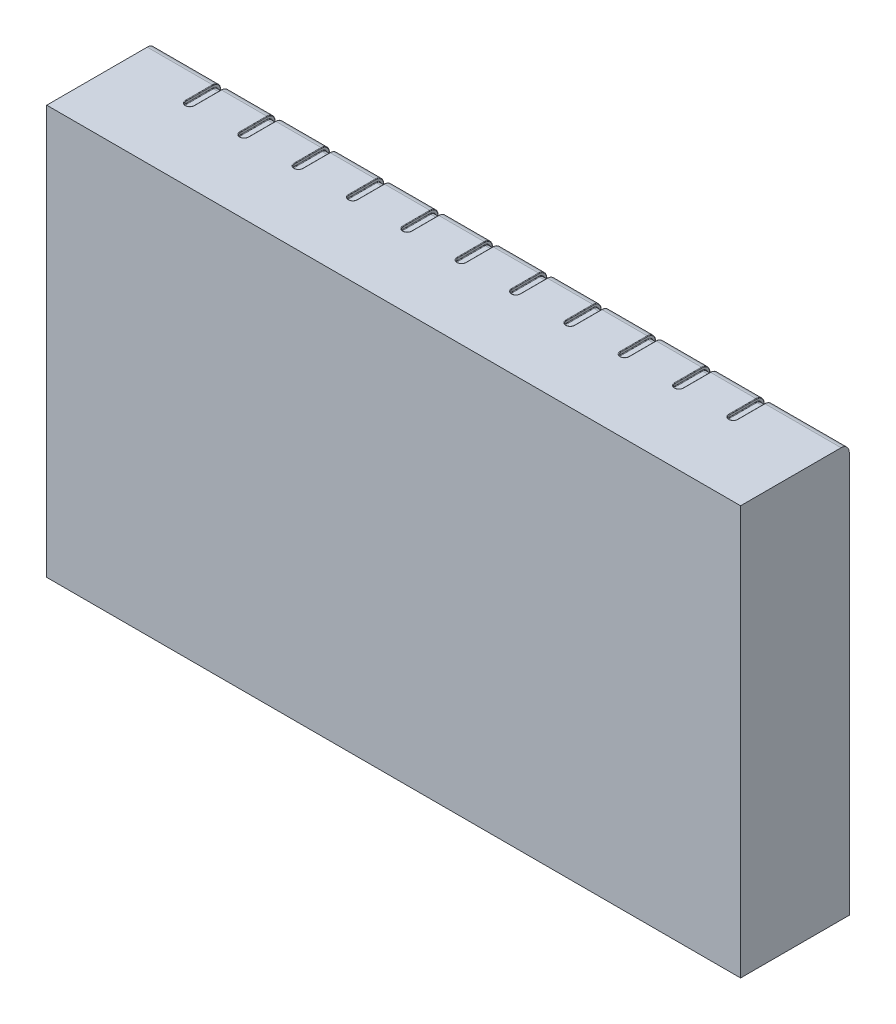
SolidWorks part; units mm, degrees
ref_plane "Plan de face" through (0, 0, 0) normal (0, 0, 1) x (1, 0, 0)
ref_plane "Plan de dessus" through (0, 0, 0) normal (0, 1, 0) x (1, 0, 0)
ref_plane "Plan de droite" through (0, 0, 0) normal (1, 0, 0) x (0, 0, -1)
sketch "Esquisse1" plane through (0, 0, 0) normal (0, 0, 1) x (1, 0, 0)
  line L1 (-127.6779, 75.255) -> (127.6779, 75.255)
  line L2 (-127.6779, 75.255) -> (-127.6779, -75.255)
  line L3 (-127.6779, -75.255) -> (127.6779, -75.255)
  line L4 (127.6779, 75.255) -> (127.6779, -75.255)
  line L5 (-127.6779, 75.255) -> (127.6779, -75.255) construction
  line L6 (-127.6779, -75.255) -> (127.6779, 75.255) construction
  point P0 (0, 0)
extrude "Boss.-Extru.1" add sketch "Esquisse1" along normal blind 40
fillet "Congé6" radius 3 1 edges at (0, 75.255, 0)
ref_plane "Plan1" through (97.6779, 0, 0) normal (1, 0, 0) x (0, 0, -1)
sketch "Esquisse2" plane through (97.6779, 0, 0) normal (1, 0, 0) x (0, 0, -1)
  line L6 (2, 72.255) -> (2, -75.255)
  line L7 (-40, 77.255) -> (-3, 77.255)
  line L8 (2, 72.255) -> (2, 62.255)
  line L9 (-13, 77.255) -> (-3, 77.255)
  line L13 (7, 82.255) -> (-13, 62.255) construction
  line L14 (7, 62.255) -> (-13, 82.255) construction
  arc A3 (2, 72.255) -> (-3, 77.255) centre (-3, 72.255) ccw
  arc A4 (2, 72.255) -> (-3, 77.255) centre (-3, 72.255) ccw
  dimension "D2" = 20
  dimension "D3" = 20
  dimension "D1" = 2
ref_plane "Plan2" through (97.6779, 77.255, 13) normal (0, 0, -1) x (-1, 0, 0)
sketch "Esquisse3" plane through (97.6779, 77.255, 13) normal (0, 0, -1) x (-1, 0, 0)
  line L1 (-1.8062, 2.8905) -> (1.1938, 2.8905)
  line L2 (-1.8062, 2.8905) -> (-1.8062, -3.1095)
  line L3 (-1.8062, -3.1095) -> (1.1938, -3.1095)
  line L4 (1.1938, 2.8905) -> (1.1938, -3.1095)
  line L5 (-1.8062, 2.8905) -> (1.1938, -3.1095) construction
  line L6 (-1.8062, -3.1095) -> (1.1938, 2.8905) construction
  point P0 (-0.3062, -0.1095)
  dimension "D1" = 3
  dimension "D2" = 6
sweep "Enlèvement de matière-Balayage1" cut profiles "Esquisse3" path "Esquisse2"
sketch "Esquisse4" plane through (0, 75.255, 0) normal (0, 1, 0) x (1, 0, 0)
  line L0 (96.4841, -13) -> (99.4841, -13) construction
  line L1 (99.4841, -13) -> (99.4841, -3) construction
  line L2 (96.4841, -3) -> (96.4841, -13) construction
  circle A0 centre (97.9841, -13) radius 1.5
extrude "Enlèv. mat.-Extru.1" cut sketch "Esquisse4" against normal up to surface (1.1095 mm away) up to face at (97.9841, 74.1454, 8)
sketch "Esquisse5" plane through (0, 0, 0) normal (0, 0, -1) x (-1, 0, 0)
  line L0 (-96.4841, 62.255) -> (-99.4841, 62.255) construction
  line L1 (-96.4841, 62.255) -> (-96.4841, 72.255) construction
  circle A0 centre (-97.9841, 62.255) radius 1.5
extrude "Enlèv. mat.-Extru.2" cut sketch "Esquisse5" against normal up to surface (1.1095 mm away) up to face at (97.9841, 67.255, 1.1095)
fillet "Congé7" radius 0.2 16 edges at (99.4841, 74.3763, 0.8787) (96.4841, 74.3763, 0.8787) (96.4841, 74.1454, 8) (99.4841, 73.5917, 1.6632) (99.4841, 67.255, 1.1095) (96.4841, 67.255, 1.1095) (96.4841, 73.5917, 1.6632) (96.4841, 75.255, 8) (96.4841, 67.255, 0) (99.4841, 75.255, 8) (99.4841, 67.255, 0) (99.4841, 74.1454, 8) (97.9841, 75.255, 14.5) (97.9841, 74.1454, 14.5) (97.9841, 60.755, 0) (97.9841, 60.755, 1.1095)
pattern_linear "Répétition linéaire2" count 11 spacing 20 along (-1, 0, 0) of "Enlèvement de matière-Balayage1", "Enlèv. mat.-Extru.1", "Enlèv. mat.-Extru.2", "Congé7"
